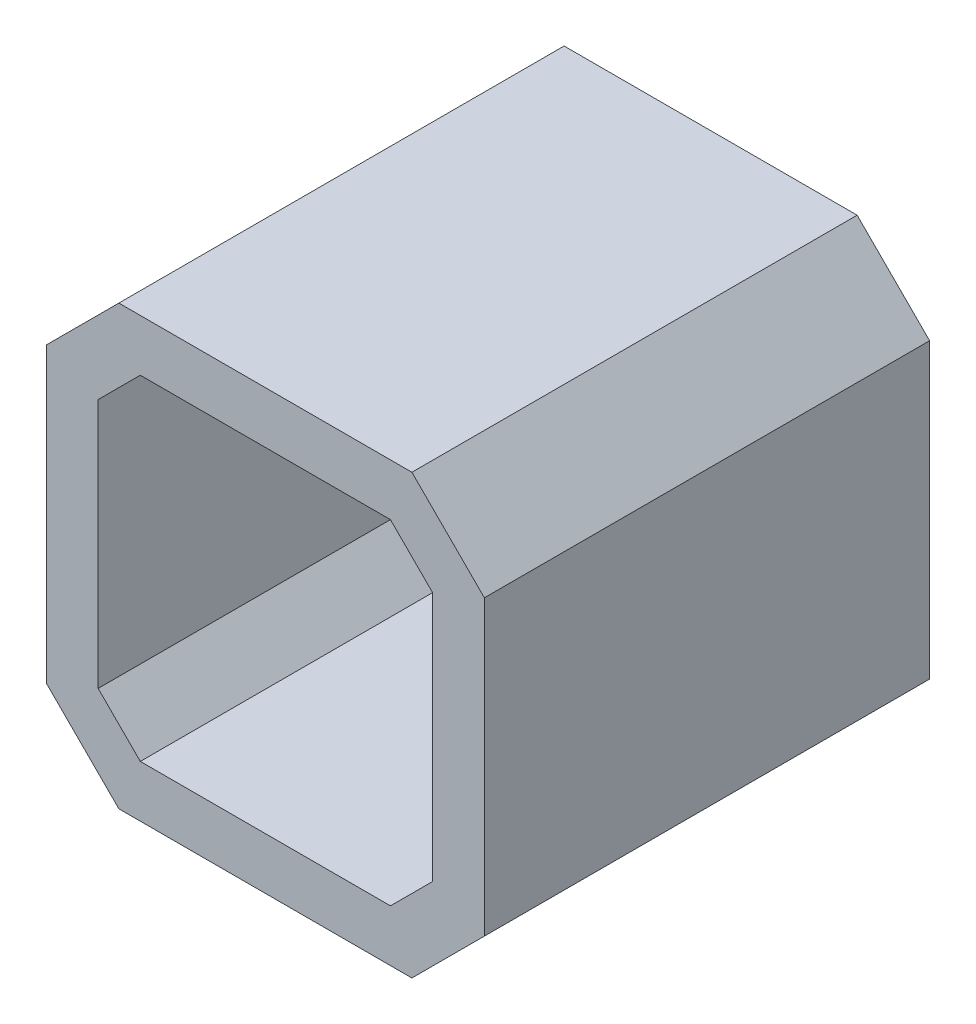
SolidWorks part; units mm, degrees
ref_plane "Front Plane" through (0, 0, 0) normal (0, 0, 1) x (1, 0, 0)
ref_plane "Top Plane" through (0, 0, 0) normal (0, 1, 0) x (1, 0, 0)
ref_plane "Right Plane" through (0, 0, 0) normal (1, 0, 0) x (0, 0, -1)
sketch "Sketch2" plane through (0, 0, 0) normal (0, 0, 1) x (1, 0, 0)
  line L0 (-21.15, 14.15) -> (-14.15, 21.15)
  line L1 (-14.15, -21.15) -> (14.15, -21.15)
  line L2 (-21.15, -14.15) -> (-21.15, 14.15)
  line L3 (-14.15, 21.15) -> (14.15, 21.15)
  line L4 (21.15, -14.15) -> (21.15, 14.15)
  line L5 (-21.15, -21.15) -> (21.15, 21.15) construction
  line L6 (-21.15, 21.15) -> (21.15, -21.15) construction
  line L7 (14.15, 21.15) -> (21.15, 14.15)
  line L8 (14.15, -21.15) -> (21.15, -14.15)
  line L9 (-21.15, -14.15) -> (-14.15, -21.15)
  line L10 (-12.0789, 16.15) -> (12.0789, 16.15)
  line L11 (12.0789, 16.15) -> (16.15, 12.0789)
  line L12 (16.15, -12.0789) -> (16.15, 12.0789)
  line L13 (12.0789, -16.15) -> (16.15, -12.0789)
  line L14 (-12.0789, -16.15) -> (12.0789, -16.15)
  line L15 (-16.15, -12.0789) -> (-12.0789, -16.15)
  line L16 (-16.15, -12.0789) -> (-16.15, 12.0789)
  line L17 (-16.15, 12.0789) -> (-12.0789, 16.15)
  point P0 (0, 0)
  dimension "D1" = 42.3
  dimension "D2" = 42.3
  dimension "D3" = 5
extrude "Boss-Extrude1" add sketch "Sketch2" along normal blind 43
